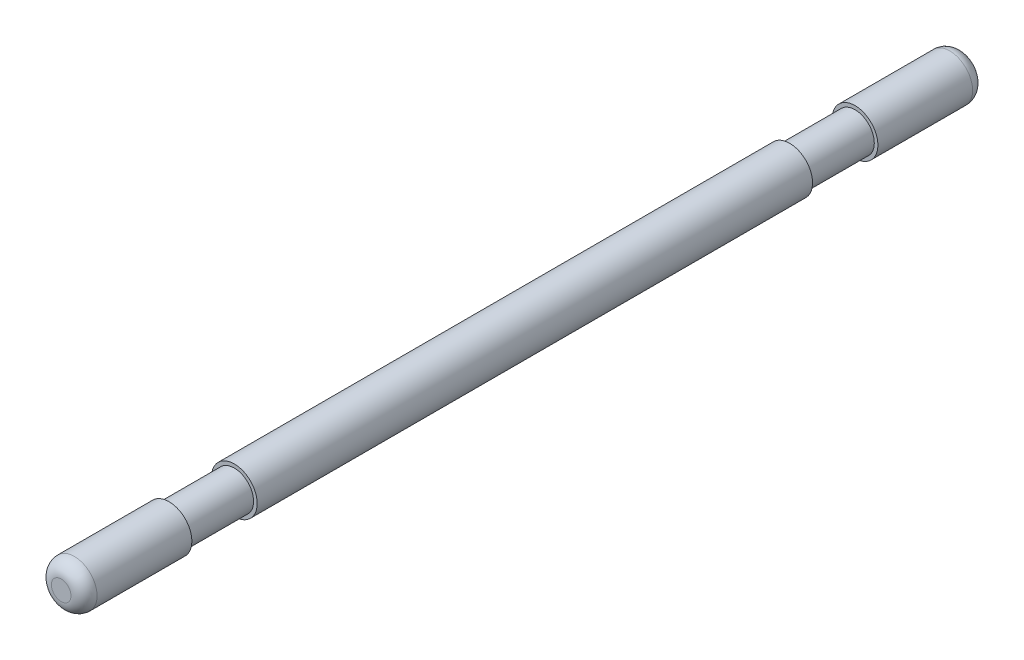
SolidWorks part; units mm, degrees
ref_plane "Front Plane" through (0, 0, 0) normal (0, 0, 1) x (1, 0, 0)
ref_plane "Top Plane" through (0, 0, 0) normal (0, 1, 0) x (1, 0, 0)
ref_plane "Right Plane" through (0, 0, 0) normal (1, 0, 0) x (0, 0, -1)
sketch "Sketch1" plane through (0, 0, 0) normal (0, 0, 1) x (1, 0, 0)
  circle A0 centre (0, 0) radius 7
  dimension "D1" = 14
extrude "Boss-Extrude1" add sketch "Sketch1" along normal mid plane 260
sketch "Sketch9" plane through (0, 0, -130) normal (0, 0, -1) x (-1, 0, 0)
  circle A0 centre (0, 0) radius 3.7592
  circle A1 centre (0, 0) radius 7
  dimension "D1" = 14
extrude "Boss-Extrude7" add sketch "Sketch9" along normal blind 5 contours A1 | A0
sketch "Sketch10" plane through (0, 0, -135) normal (0, 0, -1) x (-1, 0, 0)
  circle A0 centre (0, 0) radius 7
  dimension "D1" = 14
extrude "Boss-Extrude8" add sketch "Sketch10" along normal blind 3
fillet "Fillet6" radius 4 1 edges at (-7, 0, -138)
sketch "Sketch12" plane through (0, 0, 130) normal (0, 0, 1) x (1, 0, 0)
  circle A0 centre (0, 0) radius 2.9
  circle A1 centre (0, 0) radius 7
  dimension "D1" = 5.8
  dimension "D2" = 14
extrude "Boss-Extrude9" add sketch "Sketch12" along normal blind 5
sketch "Sketch13" plane through (0, 0, 135) normal (0, 0, 1) x (1, 0, 0)
  circle A0 centre (0, 0) radius 7
  dimension "D1" = 14
extrude "Boss-Extrude10" add sketch "Sketch13" along normal blind 3
fillet "Fillet7" radius 4 1 edges at (7, 0, 138)
sketch "Sketch14" plane through (0, 0, 0) normal (0, 1, 0) x (1, 0, 0)
  point P0 (0, 0)
  point P1 (0, 100)
  point P3 (0, -100)
  point P4 (0, -93.02)
  point P5 (0, -106.98)
  point P7 (0, 106.98)
  point P10 (0, 93.02)
  dimension "D1" = 100
  dimension "D2" = 100
  dimension "D3" = 6.98
  dimension "D4" = 6.98
  dimension "D5" = 6.98
  dimension "D6" = 6.98
ref_plane "Plane6" through (0, 0, 105) normal (0, 0, 1) x (1, 0, 0)
ref_plane "Plane7" through (0, 0, -105) normal (0, 0, 1) x (1, 0, 0)
sketch "Sketch15" plane through (0, 0, 105) normal (0, 0, 1) x (1, 0, 0)
  circle A0 centre (0, 0) radius 5.9
  circle A1 centre (0, 0) radius 7
  dimension "D1" = 11.8
extrude "Cut-Extrude1" cut sketch "Sketch15" against normal blind 20
sketch "Sketch16" plane through (0, 0, -105) normal (0, 0, 1) x (1, 0, 0)
  circle A0 centre (0, 0) radius 5.9
  circle A1 centre (0, 0) radius 7
  dimension "D1" = 11.8
extrude "Cut-Extrude2" cut sketch "Sketch16" along normal blind 20
